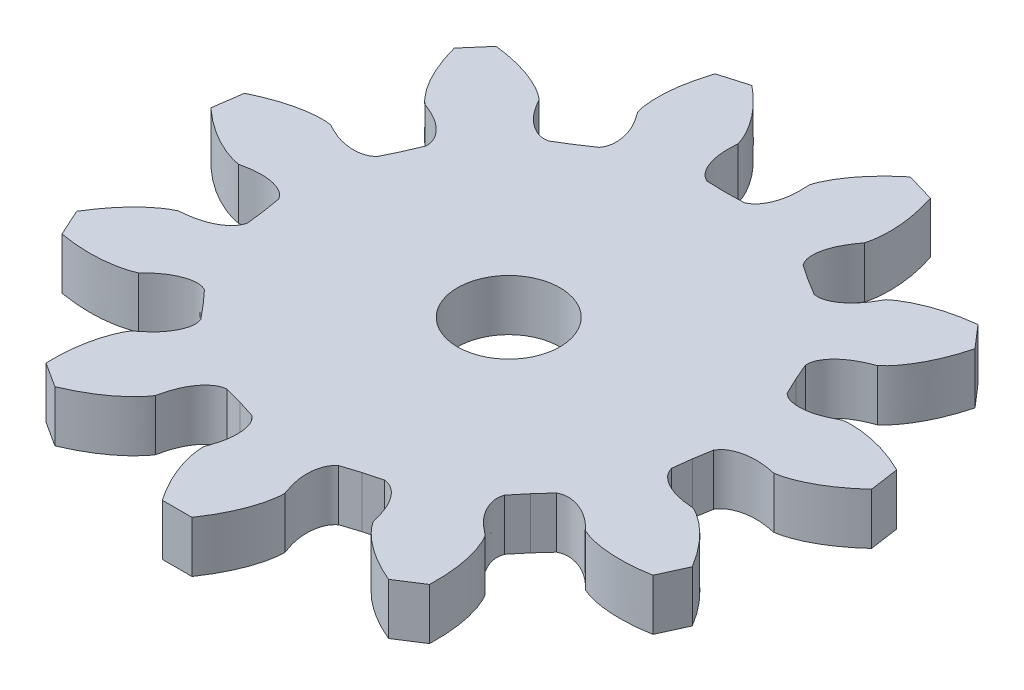
SolidWorks part; units mm, degrees
ref_plane "Plano frontal" through (0, 0, 0) normal (0, 0, 1) x (1, 0, 0)
ref_plane "Plano superior" through (0, 0, 0) normal (0, 1, 0) x (1, 0, 0)
ref_plane "Plano direito" through (0, 0, 0) normal (1, 0, 0) x (0, 0, -1)
sketch "Esboço1" plane through (0, 0, 0) normal (0, 1, 0) x (1, 0, 0)
  line L2 (-18.7943, 17.8176) -> (-20.3109, 16.0672)
  line L34 (-14.803, 8.3443) -> (-15.3728, 7.0205)
  line L35 (-15.3728, 7.0205) -> (-16.0001, 5.723)
  line L36 (-25.4437, 4.8282) -> (-25.7733, 2.5357)
  line L37 (-16.9643, -0.9835) -> (-16.728, -2.4051)
  line L38 (-16.728, -2.4051) -> (-16.5542, -3.8358)
  line L39 (-24.0149, -9.6942) -> (-23.0528, -11.8009)
  line L40 (-13.7396, -9.999) -> (-12.7722, -11.0671)
  line L41 (-12.7722, -11.0671) -> (-11.8525, -12.1768)
  line L42 (-14.9615, -21.1387) -> (-13.0132, -22.3908)
  line L43 (-6.1526, -15.8399) -> (-4.7613, -16.2154)
  line L44 (-4.7613, -16.2154) -> (-3.3877, -16.6517)
  line L45 (-1.158, -25.8718) -> (1.158, -25.8718)
  line L46 (3.3877, -16.6517) -> (4.7613, -16.2154)
  line L47 (4.7613, -16.2154) -> (6.1526, -15.8399)
  line L48 (13.0132, -22.3908) -> (14.9615, -21.1387)
  line L49 (11.8525, -12.1768) -> (12.7721, -11.0671)
  line L50 (12.7721, -11.0671) -> (13.7396, -9.999)
  line L51 (23.0528, -11.8009) -> (24.0149, -9.6942)
  line L52 (16.5542, -3.8358) -> (16.728, -2.4051)
  line L53 (16.728, -2.4051) -> (16.9643, -0.9835)
  line L54 (25.7733, 2.5357) -> (25.4437, 4.8282)
  line L55 (16.0001, 5.723) -> (15.3728, 7.0205)
  line L56 (15.3728, 7.0205) -> (14.803, 8.3443)
  line L57 (20.3109, 16.0672) -> (18.7943, 17.8176)
  line L58 (10.366, 13.4648) -> (9.1368, 14.2172)
  line L59 (9.1368, 14.2172) -> (7.9418, 15.0228)
  line L60 (8.4, 24.4976) -> (6.1778, 25.1501)
  line L61 (1.4408, 16.9316) -> (0, 16.9)
  line L62 (0, 16.9) -> (-1.4408, 16.9316)
  line L63 (-6.1778, 25.1501) -> (-8.4, 24.4976)
  line L64 (-7.9418, 15.0228) -> (-9.1368, 14.2172)
  line L65 (-9.1368, 14.2172) -> (-10.366, 13.4648)
  circle A0 centre (0, 0) radius 4
  spline S88 degree 3 poles (-13.523, 15.8987) (-13.8763, 16.2077) (-14.6829, 16.7037) (-16.4426, 17.4249) (-17.8516, 17.711) (-18.7943, 17.8176) knots 0.002943 0.002943 0.002943 0.002943 0.249944 0.496944 0.990944 0.990944 0.990944 0.990944
  spline S89 degree 3 poles (-20.3109, 16.0672) (-20.0713, 15.1494) (-19.5875, 13.7954) (-18.6233, 12.1563) (-18.0175, 11.4285) (-17.6614, 11.1227) knots 0.009056 0.009056 0.009056 0.009056 0.503056 0.750056 0.997057 0.997057 0.997057 0.997057
  spline S90 degree 3 poles (-17.6614, 11.1227) (-17.3384, 10.9973) (-16.6949, 10.7416) (-15.8016, 10.1766) (-15.1821, 9.5392) (-14.8863, 8.9766) (-14.8068, 8.6145) (-14.8044, 8.4345) (-14.803, 8.3443) knots 0.00416 0.00416 0.00416 0.00416 0.254422 0.504683 0.754944 0.880075 0.94264 1.005205 1.005205 1.005205 1.005205
  spline S91 degree 3 poles (-16.0001, 5.723) (-16.0692, 5.665) (-16.2068, 5.5489) (-16.5325, 5.3719) (-17.1514, 5.227) (-18.0388, 5.2777) (-19.0508, 5.5829) (-19.6655, 5.9018) (-19.9718, 6.0638) knots -0.005205 -0.005205 -0.005205 -0.005205 0.05736 0.119925 0.245056 0.495317 0.745578 0.99584 0.99584 0.99584 0.99584
  spline S92 degree 3 poles (-19.9718, 6.0638) (-20.436, 6.1327) (-21.3827, 6.1139) (-23.2529, 5.7692) (-24.593, 5.2481) (-25.4437, 4.8282) knots 0.002943 0.002943 0.002943 0.002943 0.249944 0.496944 0.990944 0.990944 0.990944 0.990944
  spline S93 degree 3 poles (-25.7733, 2.5357) (-25.0754, 1.8931) (-23.9364, 1.0156) (-22.2391, 0.158) (-21.336, -0.1268) (-20.8711, -0.1914) knots 0.009056 0.009056 0.009056 0.009056 0.503056 0.750056 0.997057 0.997057 0.997057 0.997057
  spline S94 degree 3 poles (-20.8711, -0.1914) (-20.5316, -0.1224) (-19.852, 0.0105) (-18.795, 0.0182) (-17.9292, -0.1832) (-17.3762, -0.4965) (-17.1136, -0.7582) (-17.0143, -0.9083) (-16.9643, -0.9835) knots 0.00416 0.00416 0.00416 0.00416 0.254422 0.504683 0.754944 0.880075 0.94264 1.005205 1.005205 1.005205 1.005205
  spline S95 degree 3 poles (-16.5542, -3.8358) (-16.581, -3.922) (-16.634, -4.094) (-16.8123, -4.419) (-17.2546, -4.8755) (-18.0286, -5.3126) (-19.0449, -5.603) (-19.7344, -5.667) (-20.0796, -5.6964) knots -0.005205 -0.005205 -0.005205 -0.005205 0.05736 0.119925 0.245056 0.495317 0.745578 0.99584 0.99584 0.99584 0.99584
  spline S96 degree 3 poles (-20.0796, -5.6964) (-20.5075, -5.8894) (-21.2937, -6.4171) (-22.6807, -7.7181) (-23.5263, -8.881) (-24.0149, -9.6942) knots 0.002943 0.002943 0.002943 0.002943 0.249944 0.496944 0.990944 0.990944 0.990944 0.990944
  spline S97 degree 3 poles (-23.0528, -11.8009) (-22.1183, -11.9642) (-20.6857, -12.0866) (-18.7941, -11.8904) (-17.8805, -11.6418) (-17.4544, -11.4448) knots 0.009056 0.009056 0.009056 0.009056 0.503056 0.750056 0.997057 0.997057 0.997057 0.997057
  spline S98 degree 3 poles (-17.4544, -11.4448) (-17.2062, -11.2032) (-16.7062, -10.724) (-15.8212, -10.1461) (-14.984, -9.8474) (-14.3494, -9.812) (-13.987, -9.8901) (-13.8223, -9.9627) (-13.7396, -9.999) knots 0.00416 0.00416 0.00416 0.00416 0.254422 0.504683 0.754944 0.880075 0.94264 1.005205 1.005205 1.005205 1.005205
  spline S99 degree 3 poles (-11.8525, -12.1768) (-11.8285, -12.2638) (-11.78, -12.4371) (-11.7543, -12.8069) (-11.8796, -13.43) (-12.2944, -14.2162) (-12.9924, -15.01) (-13.5378, -15.4366) (-13.8124, -15.648) knots -0.005205 -0.005205 -0.005205 -0.005205 0.05736 0.119925 0.245056 0.495317 0.745578 0.99584 0.99584 0.99584 0.99584
  spline S100 degree 3 poles (-13.8124, -15.648) (-14.0679, -16.0417) (-14.4441, -16.9106) (-14.9075, -18.755) (-14.9902, -20.1904) (-14.9615, -21.1387) knots 0.002943 0.002943 0.002943 0.002943 0.249944 0.496944 0.990944 0.990944 0.990944 0.990944
  spline S101 degree 3 poles (-13.0132, -22.3908) (-12.1387, -22.023) (-10.8674, -21.3514) (-9.3822, -20.1637) (-8.748, -19.4606) (-8.496, -19.0646) knots 0.009056 0.009056 0.009056 0.009056 0.503056 0.750056 0.997057 0.997057 0.997057 0.997057
  spline S102 degree 3 poles (-8.496, -19.0646) (-8.4179, -18.727) (-8.2564, -18.0537) (-7.8243, -17.089) (-7.2814, -16.3851) (-6.7667, -16.0123) (-6.4196, -15.882) (-6.2418, -15.8541) (-6.1526, -15.8399) knots 0.00416 0.00416 0.00416 0.00416 0.254422 0.504683 0.754944 0.880075 0.94264 1.005205 1.005205 1.005205 1.005205
  spline S103 degree 3 poles (-3.3877, -16.6517) (-3.3204, -16.7119) (-3.186, -16.8315) (-2.9644, -17.1287) (-2.7329, -17.7207) (-2.6568, -18.6063) (-2.8149, -19.6514) (-3.0431, -20.3052) (-3.1598, -20.6314) knots -0.005205 -0.005205 -0.005205 -0.005205 0.05736 0.119925 0.245056 0.495317 0.745578 0.99584 0.99584 0.99584 0.99584
  spline S104 degree 3 poles (-3.1598, -20.6314) (-3.1619, -21.1008) (-3.0086, -22.0352) (-2.4012, -23.8373) (-1.6948, -25.0896) (-1.158, -25.8718) knots 0.002943 0.002943 0.002943 0.002943 0.249944 0.496944 0.990944 0.990944 0.990944 0.990944
  spline S105 degree 3 poles (1.158, -25.8718) (1.6948, -25.0896) (2.4012, -23.8373) (3.0086, -22.0352) (3.1619, -21.1008) (3.1598, -20.6314) knots 0.009056 0.009056 0.009056 0.009056 0.503056 0.750056 0.997057 0.997057 0.997057 0.997057
  spline S106 degree 3 poles (3.1598, -20.6314) (3.0431, -20.3052) (2.8149, -19.6514) (2.6568, -18.6063) (2.7329, -17.7207) (2.9644, -17.1287) (3.186, -16.8315) (3.3204, -16.7119) (3.3877, -16.6517) knots 0.00416 0.00416 0.00416 0.00416 0.254422 0.504683 0.754944 0.880075 0.94264 1.005205 1.005205 1.005205 1.005205
  spline S107 degree 3 poles (6.1526, -15.8399) (6.2418, -15.8541) (6.4196, -15.882) (6.7667, -16.0123) (7.2814, -16.3851) (7.8243, -17.089) (8.2563, -18.0537) (8.4178, -18.727) (8.496, -19.0646) knots -0.005205 -0.005205 -0.005205 -0.005205 0.05736 0.119925 0.245056 0.495317 0.745578 0.99584 0.99584 0.99584 0.99584
  spline S108 degree 3 poles (8.496, -19.0646) (8.748, -19.4606) (9.3822, -20.1637) (10.8674, -21.3514) (12.1387, -22.023) (13.0132, -22.3908) knots 0.002943 0.002943 0.002943 0.002943 0.249944 0.496944 0.990944 0.990944 0.990944 0.990944
  spline S109 degree 3 poles (14.9615, -21.1387) (14.9902, -20.1904) (14.9075, -18.755) (14.4441, -16.9106) (14.0679, -16.0417) (13.8124, -15.648) knots 0.009056 0.009056 0.009056 0.009056 0.503056 0.750056 0.997057 0.997057 0.997057 0.997057
  spline S110 degree 3 poles (13.8124, -15.648) (13.5378, -15.4366) (12.9924, -15.01) (12.2944, -14.2162) (11.8796, -13.43) (11.7543, -12.8069) (11.78, -12.4371) (11.8284, -12.2638) (11.8525, -12.1768) knots 0.00416 0.00416 0.00416 0.00416 0.254422 0.504683 0.754944 0.880075 0.94264 1.005205 1.005205 1.005205 1.005205
  spline S111 degree 3 poles (13.7396, -9.999) (13.8223, -9.9627) (13.987, -9.8901) (14.3494, -9.812) (14.984, -9.8474) (15.8212, -10.1461) (16.7062, -10.724) (17.2062, -11.2032) (17.4544, -11.4448) knots -0.005205 -0.005205 -0.005205 -0.005205 0.05736 0.119925 0.245056 0.495317 0.745578 0.99584 0.99584 0.99584 0.99584
  spline S112 degree 3 poles (17.4544, -11.4448) (17.8805, -11.6418) (18.7941, -11.8904) (20.6857, -12.0866) (22.1183, -11.9642) (23.0528, -11.8009) knots 0.002943 0.002943 0.002943 0.002943 0.249944 0.496944 0.990944 0.990944 0.990944 0.990944
  spline S113 degree 3 poles (24.0149, -9.6942) (23.5263, -8.881) (22.6807, -7.7181) (21.2937, -6.4171) (20.5075, -5.8894) (20.0796, -5.6964) knots 0.009056 0.009056 0.009056 0.009056 0.503056 0.750056 0.997057 0.997057 0.997057 0.997057
  spline S114 degree 3 poles (20.0796, -5.6964) (19.7344, -5.667) (19.0449, -5.603) (18.0286, -5.3126) (17.2546, -4.8755) (16.8123, -4.419) (16.634, -4.094) (16.581, -3.922) (16.5542, -3.8358) knots 0.00416 0.00416 0.00416 0.00416 0.254422 0.504683 0.754944 0.880075 0.94264 1.005205 1.005205 1.005205 1.005205
  spline S115 degree 3 poles (16.9643, -0.9835) (17.0143, -0.9083) (17.1136, -0.7582) (17.3762, -0.4965) (17.9292, -0.1832) (18.795, 0.0182) (19.852, 0.0105) (20.5316, -0.1224) (20.8711, -0.1914) knots -0.005205 -0.005205 -0.005205 -0.005205 0.05736 0.119925 0.245056 0.495317 0.745578 0.99584 0.99584 0.99584 0.99584
  spline S116 degree 3 poles (20.8711, -0.1914) (21.336, -0.1268) (22.2391, 0.158) (23.9364, 1.0156) (25.0754, 1.8931) (25.7733, 2.5357) knots 0.002943 0.002943 0.002943 0.002943 0.249944 0.496944 0.990944 0.990944 0.990944 0.990944
  spline S117 degree 3 poles (25.4437, 4.8282) (24.593, 5.2481) (23.2529, 5.7692) (21.3827, 6.1139) (20.436, 6.1327) (19.9718, 6.0638) knots 0.009056 0.009056 0.009056 0.009056 0.503056 0.750056 0.997057 0.997057 0.997057 0.997057
  spline S118 degree 3 poles (19.9718, 6.0638) (19.6655, 5.9018) (19.0508, 5.5829) (18.0388, 5.2777) (17.1514, 5.227) (16.5325, 5.3719) (16.2068, 5.5489) (16.0692, 5.665) (16.0001, 5.723) knots 0.00416 0.00416 0.00416 0.00416 0.254422 0.504683 0.754944 0.880075 0.94264 1.005205 1.005205 1.005205 1.005205
  spline S119 degree 3 poles (14.803, 8.3443) (14.8044, 8.4345) (14.8068, 8.6145) (14.8863, 8.9766) (15.1821, 9.5392) (15.8016, 10.1766) (16.6949, 10.7416) (17.3385, 10.9973) (17.6614, 11.1227) knots -0.005205 -0.005205 -0.005205 -0.005205 0.05736 0.119925 0.245056 0.495317 0.745578 0.99584 0.99584 0.99584 0.99584
  spline S120 degree 3 poles (17.6614, 11.1227) (18.0175, 11.4285) (18.6233, 12.1563) (19.5875, 13.7954) (20.0713, 15.1494) (20.3109, 16.0672) knots 0.002943 0.002943 0.002943 0.002943 0.249944 0.496944 0.990944 0.990944 0.990944 0.990944
  spline S121 degree 3 poles (18.7943, 17.8176) (17.8516, 17.711) (16.4426, 17.4248) (14.6829, 16.7037) (13.8763, 16.2077) (13.523, 15.8987) knots 0.009056 0.009056 0.009056 0.009056 0.503056 0.750056 0.997057 0.997057 0.997057 0.997057
  spline S122 degree 3 poles (13.523, 15.8987) (13.3529, 15.5969) (13.0082, 14.9963) (12.3219, 14.1924) (11.6027, 13.67) (11.0038, 13.4573) (10.6341, 13.4301) (10.4556, 13.4534) (10.366, 13.4648) knots 0.00416 0.00416 0.00416 0.00416 0.254422 0.504683 0.754944 0.880075 0.94264 1.005205 1.005205 1.005205 1.005205
  spline S123 degree 3 poles (7.9418, 15.0228) (7.8942, 15.0995) (7.7989, 15.2521) (7.67, 15.5997) (7.6147, 16.2329) (7.7912, 17.1041) (8.2373, 18.0624) (8.6404, 18.6254) (8.8443, 18.9055) knots -0.005205 -0.005205 -0.005205 -0.005205 0.05736 0.119925 0.245056 0.495317 0.745578 0.99584 0.99584 0.99584 0.99584
  spline S124 degree 3 poles (8.8443, 18.9055) (8.9786, 19.3553) (9.0947, 20.295) (9.0197, 22.1952) (8.6947, 23.5958) (8.4, 24.4976) knots 0.002943 0.002943 0.002943 0.002943 0.249944 0.496944 0.990944 0.990944 0.990944 0.990944
  spline S125 degree 3 poles (6.1778, 25.1501) (5.4424, 24.5508) (4.4118, 23.5482) (3.3213, 21.9902) (2.911, 21.1369) (2.7808, 20.6859) knots 0.009056 0.009056 0.009056 0.009056 0.503056 0.750056 0.997057 0.997057 0.997057 0.997057
  spline S126 degree 3 poles (2.7808, 20.6859) (2.8008, 20.3401) (2.8356, 19.6485) (2.6928, 18.6011) (2.3703, 17.7728) (1.9814, 17.2701) (1.6851, 17.0473) (1.5223, 16.9704) (1.4408, 16.9316) knots 0.00416 0.00416 0.00416 0.00416 0.254422 0.504683 0.754944 0.880075 0.94264 1.005205 1.005205 1.005205 1.005205
  spline S127 degree 3 poles (-1.4408, 16.9316) (-1.5223, 16.9704) (-1.6851, 17.0473) (-1.9814, 17.2701) (-2.3703, 17.7728) (-2.6928, 18.6011) (-2.8356, 19.6485) (-2.8008, 20.3401) (-2.7808, 20.6859) knots -0.005205 -0.005205 -0.005205 -0.005205 0.05736 0.119925 0.245056 0.495317 0.745578 0.99584 0.99584 0.99584 0.99584
  spline S128 degree 3 poles (-2.7808, 20.6859) (-2.911, 21.1369) (-3.3213, 21.9902) (-4.4118, 23.5482) (-5.4424, 24.5508) (-6.1778, 25.1501) knots 0.002943 0.002943 0.002943 0.002943 0.249944 0.496944 0.990944 0.990944 0.990944 0.990944
  spline S129 degree 3 poles (-8.4, 24.4976) (-8.6947, 23.5958) (-9.0197, 22.1952) (-9.0947, 20.295) (-8.9786, 19.3553) (-8.8443, 18.9055) knots 0.009056 0.009056 0.009056 0.009056 0.503056 0.750056 0.997057 0.997057 0.997057 0.997057
  spline S130 degree 3 poles (-8.8443, 18.9055) (-8.6404, 18.6254) (-8.2373, 18.0624) (-7.7912, 17.1041) (-7.6147, 16.2329) (-7.67, 15.5997) (-7.7989, 15.2521) (-7.8942, 15.0995) (-7.9418, 15.0228) knots 0.00416 0.00416 0.00416 0.00416 0.254422 0.504683 0.754944 0.880075 0.94264 1.005205 1.005205 1.005205 1.005205
  spline S131 degree 3 poles (-10.366, 13.4648) (-10.4556, 13.4534) (-10.6341, 13.4301) (-11.0038, 13.4573) (-11.6027, 13.67) (-12.3219, 14.1924) (-13.0082, 14.9963) (-13.3529, 15.5969) (-13.523, 15.8987) knots -0.005205 -0.005205 -0.005205 -0.005205 0.05736 0.119925 0.245056 0.495317 0.745578 0.99584 0.99584 0.99584 0.99584
  point P93 (0, 0)
  dimension "D1" = 11
extrude "Ressalto-extrusão1" add sketch "Esboço1" along normal blind 4
